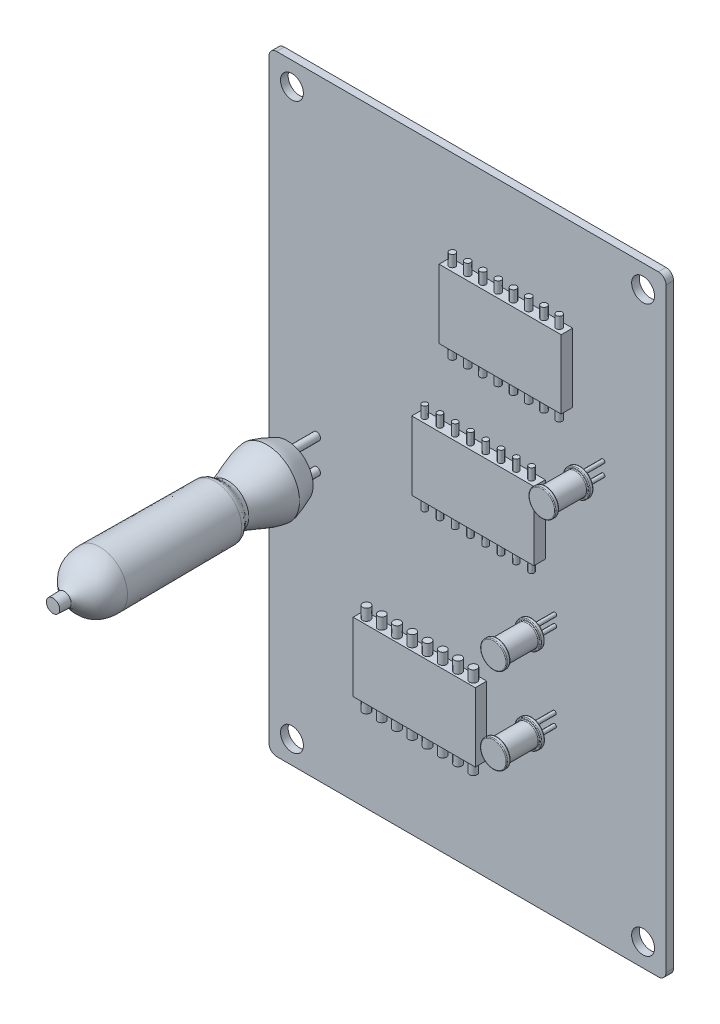
SolidWorks part; units mm, degrees
ref_plane "Plan de face" through (0, 0, 0) normal (0, 0, 1) x (1, 0, 0)
ref_plane "Plan de dessus" through (0, 0, 0) normal (0, 1, 0) x (1, 0, 0)
ref_plane "Plan de droite" through (0, 0, 0) normal (1, 0, 0) x (0, 0, -1)
sketch "Esquisse1" plane through (0, 0, 0) normal (0, 0, 1) x (1, 0, 0)
  line L0 (0, 49.3082) -> (0, -52.8302) construction
  line L1 (50.7838, 0) -> (-60.1596, 0) construction
  line L2 (-25, 40) -> (25, 40)
  line L3 (26, 39) -> (26, -39)
  line L4 (-26, 39) -> (-26, -39)
  line L5 (-25, -40) -> (25, -40)
  circle A0 centre (-23, 37) radius 1.5
  circle A1 centre (23, 37) radius 1.5
  circle A2 centre (23, -37) radius 1.5
  circle A3 centre (-23, -37) radius 1.5
  arc A4 (-25, -40) -> (-26, -39) centre (-25, -39) cw
  arc A5 (25, -40) -> (26, -39) centre (25, -39) ccw
  arc A6 (25, 40) -> (26, 39) centre (25, 39) cw
  arc A7 (-26, 39) -> (-25, 40) centre (-25, 39) cw
  point P8 (0, -40)
  point P10 (0, 40)
  point P11 (-26, 0)
  point P12 (26, 0)
  point P23 (-26, -40)
  point P26 (26, -40)
  point P29 (26, 40)
  point P32 (-26, 40)
  dimension "D2" = 3
  dimension "D1" = 1
extrude "Boss.-Extru.1" add sketch "Esquisse1" along normal blind 1
sketch3d "Esquisse3D1"
  line L0 (-19.7618, -3.0052, 3.4506) -> (-19.7618, -3.0052, 38.1154) construction
ref_plane "Plan1" through (-19.7618, 0, 0) normal (-1, 0, 0) x (0, 0, 1)
sketch "Esquisse2" plane through (-19.7618, 0, 0) normal (-1, 0, 0) x (0, 0, 1)
  line L0 (38.1154, -3.0052) -> (3.4506, -3.0052) construction
  line L1 (4.8485, -6.3885) -> (4.8485, -3.0052)
  line L2 (35.5477, -3.0052) -> (4.8485, -3.0052)
  spline S0 degree 1 poles (35.5477, -3.0052) (35.531, -3.8812) knots 0 0 1 1
  spline S1 degree 2 poles (35.531, -3.8812) (34.9031, -3.9149) (34.078, -3.932) knots 0 0 0 1 1 1
  spline S2 degree 3 poles (34.078, -3.932) (32.9893, -4.1971) (32.7481, -6.6831) (29.4085, -6.6295) knots 0 0 0 0 1 1 1 1
  spline S3 degree 1 poles (29.4085, -6.6295) (14.3307, -6.5217) knots 0 0 1 1
  spline S4 degree 3 poles (14.3307, -6.5217) (13.438, -6.5319) (13.6441, -5.8174) (12.6297, -5.7462) knots 0 0 0 0 1 1 1 1
  spline S5 degree 3 poles (12.6297, -5.7462) (11.6687, -5.8352) (9.4972, -7.0557) (7.5104, -7.2675) knots 0 0 0 0 1 1 1 1
  spline S6 degree 3 poles (7.5104, -7.2675) (6.8891, -7.2309) (5.3946, -6.5858) (4.8485, -6.3885) knots 0 0 0 0 1 1 1 1
revolve "Révolution1" add sketch "Esquisse2" angle 360 about L2
sketch "Esquisse3" plane through (0, 0, 4.8485) normal (0, 0, -1) x (-1, 0, 0)
  line L0 (19.7618, -6.3885) -> (19.7618, 0.5651) construction
  line L1 (23.0053, -3.0052) -> (16.3785, -3.0052) construction
  circle A0 centre (19.7618, -3.0052) radius 3.3833 construction
  circle A1 centre (19.7618, -1.023) radius 0.5
  circle A2 centre (19.7618, -4.9874) radius 0.5
  dimension "D1" = 1
extrude "Boss.-Extru.2" add sketch "Esquisse3" along normal blind 5
sketch "Esquisse4" plane through (0, 0, 1) normal (0, 0, 1) x (1, 0, 0)
  line L1 (13.7698, 27.9997) -> (-2.2302, 27.9997)
  line L2 (13.7698, 27.9997) -> (13.7698, 18.9997)
  line L3 (13.7698, 18.9997) -> (-2.2302, 18.9997)
  line L4 (-2.2302, 27.9997) -> (-2.2302, 18.9997)
  line L5 (10.1949, 9) -> (-5.8051, 9)
  line L6 (10.1949, 9) -> (10.1949, 0)
  line L7 (10.1949, 0) -> (-5.8051, 0)
  line L8 (-5.8051, 9) -> (-5.8051, 0)
  line L9 (2.5156, -17.6757) -> (-13.4844, -17.6757)
  line L10 (2.5156, -17.6757) -> (2.5156, -26.679)
  line L11 (2.5156, -26.679) -> (-13.4844, -26.679)
  line L12 (-13.4844, -17.6757) -> (-13.4844, -26.679)
  dimension "D1" = 9.0033
  dimension "D2" = 9
  dimension "D3" = 9
  dimension "D4" = 16
  dimension "D5" = 16
  dimension "D6" = 16
extrude "Boss.-Extru.3" add sketch "Esquisse4" along normal blind 1.5
sketch "Esquisse5" plane through (0, -26.679, 0) normal (0, -1, 0) x (1, 0, 0)
  line L1 (2.5156, 1.75) -> (-5.4844, 1.75) construction
  line L2 (2.5156, 2.5) -> (2.5156, 1) construction
  circle A0 centre (-4.4844, 1.75) radius 0.5
  circle A1 centre (-2.4844, 1.75) radius 0.5
  circle A2 centre (-0.4844, 1.75) radius 0.5
  circle A3 centre (1.5156, 1.75) radius 0.5
  circle A4 centre (-12.4844, 1.75) radius 0.5
  circle A5 centre (-10.4844, 1.75) radius 0.5
  circle A6 centre (-8.4844, 1.75) radius 0.5
  circle A7 centre (-6.4844, 1.75) radius 0.5
  dimension "D3" = 4
extrude "Boss.-Extru.4" add sketch "Esquisse5" along normal blind 1.5 and the other way blind 10.5
sketch "Esquisse6" plane through (0, 0, 0) normal (0, -1, 0) x (1, 0, 0)
  line L0 (2.1949, 5.3342) -> (2.1949, -1.5605) construction
  line L1 (10.9215, 1.8041) -> (1.2414, 1.8041) construction
  circle A0 centre (3.1949, 1.8041) radius 0.3538
  circle A1 centre (5.1949, 1.8041) radius 0.3538
  circle A2 centre (7.1949, 1.8041) radius 0.3538
  circle A3 centre (9.1949, 1.8041) radius 0.3538
  circle A4 centre (-4.8051, 1.8041) radius 0.3538
  circle A5 centre (-2.8051, 1.8041) radius 0.3538
  circle A6 centre (-0.8051, 1.8041) radius 0.3538
  circle A7 centre (1.1949, 1.8041) radius 0.3538
  dimension "D1" = 1
  dimension "D2" = 4
extrude "Boss.-Extru.5" add sketch "Esquisse6" along normal blind 1.5 and the other way blind 10.5
sketch "Esquisse7" plane through (0, 18.9997, 0) normal (0, -1, 0) x (1, 0, 0)
  line L0 (5.7698, 4.6078) -> (5.7698, -2.5835) construction
  line L1 (15.0689, 1.75) -> (4.3918, 1.75) construction
  circle A0 centre (6.7698, 1.75) radius 0.4
  circle A1 centre (8.7698, 1.75) radius 0.4
  circle A2 centre (10.7698, 1.75) radius 0.4
  circle A3 centre (12.7698, 1.75) radius 0.4
  circle A4 centre (-1.2302, 1.75) radius 0.4
  circle A5 centre (0.7698, 1.75) radius 0.4
  circle A6 centre (2.7698, 1.75) radius 0.4
  circle A7 centre (4.7698, 1.75) radius 0.4
  dimension "D1" = 0.8
  dimension "D2" = 1
  dimension "D3" = 4
extrude "Boss.-Extru.6" add sketch "Esquisse7" along normal blind 1.5 and the other way blind 10.5
sketch "Esquisse8" plane through (0, 0, 1) normal (0, 0, 1) x (1, 0, 0)
  circle A0 centre (11.3866, -17.5433) radius 1.75
  circle A1 centre (11.3866, -6.2891) radius 1.725
  circle A2 centre (17.7419, 14.1008) radius 1.75
  dimension "D1" = 3.5
  dimension "D2" = 3.45
  dimension "D3" = 3.5
extrude "Boss.-Extru.7" add sketch "Esquisse8" along normal blind 0.5 from offset 3 separate body
sketch "Esquisse9" plane through (0, 0, 4.5) normal (0, 0, 1) x (1, 0, 0)
  circle A9 centre (17.7419, 14.1008) radius 1.45
  circle A10 centre (11.3866, -6.2891) radius 1.425
  circle A11 centre (11.3866, -17.5433) radius 1.45
extrude "Boss.-Extru.8" add sketch "Esquisse9" along normal blind 4
sketch "Esquisse10" plane through (0, 0, 8.5) normal (0, 0, 1) x (1, 0, 0)
  circle A6 centre (11.3866, -6.2891) radius 1.725
  circle A7 centre (11.3866, -17.5433) radius 1.75
  circle A8 centre (17.7419, 14.1008) radius 1.75
extrude "Boss.-Extru.9" add sketch "Esquisse10" along normal blind 0.5
fillet "Congé1" radius 0.1 4 edges at (19.4919, 14.1008, 8.5) (19.4919, 14.1008, 9) (19.4919, 14.1008, 4) (19.4919, 14.1008, 4.5)
fillet "Congé2" radius 0.1 4 edges at (13.1116, -6.2891, 8.5) (13.1116, -6.2891, 9) (13.1116, -6.2891, 4) (13.1116, -6.2891, 4.5)
fillet "Congé3" radius 0.1 4 edges at (13.1366, -17.5433, 4) (13.1366, -17.5433, 4.5) (13.1366, -17.5433, 8.5) (13.1366, -17.5433, 9)
sketch "Esquisse11" plane through (0, 0, 4) normal (0, 0, -1) x (-1, 0, 0)
  line L0 (-17.7419, 15.7508) -> (-17.7419, 12.4508) construction
  line L1 (-19.3919, 14.1008) -> (-16.0919, 14.1008) construction
  circle A0 centre (-17.7419, 14.1008) radius 1.65 construction
  circle A1 centre (-17.7419, 13.3045) radius 0.25
  circle A2 centre (-17.7419, 14.8971) radius 0.25
  dimension "D1" = 0.5
extrude "Boss.-Extru.10" add sketch "Esquisse11" along normal up to next (3 mm away)
fillet "Congé4" radius 0.1 2 edges at (19.1919, 14.1008, 4.5) (19.1919, 14.1008, 8.5)
fillet "Congé5" radius 0.1 2 edges at (12.8116, -6.2891, 4.5) (12.8116, -6.2891, 8.5)
fillet "Congé6" radius 0.1 2 edges at (12.8366, -17.5433, 4.5) (12.8366, -17.5433, 8.5)
sketch "Esquisse12" plane through (0, 0, 4) normal (0, 0, -1) x (-1, 0, 0)
  line L0 (-11.3244, -4.6653) -> (-11.4801, -7.9114) construction
  line L1 (-13.0116, -6.2891) -> (-9.844, -6.2891) construction
  circle A0 centre (-11.3866, -6.2891) radius 1.625 construction
  circle A1 centre (-11.4335, -6.9392) radius 0.25
  circle A2 centre (-11.4335, -5.639) radius 0.25
  dimension "D1" = 0.5
extrude "Boss.-Extru.11" add sketch "Esquisse12" along normal up to next
sketch "Esquisse14" plane through (0, 0, 4) normal (0, 0, -1) x (-1, 0, 0)
  line L0 (-13.0366, -17.5433) -> (-9.6844, -17.5751) construction
  line L1 (-11.3866, -15.8933) -> (-11.3866, -19.1933) construction
  circle A0 centre (-11.3866, -17.5433) radius 1.65 construction
  circle A1 centre (-11.3866, -18.3044) radius 0.25
  circle A2 centre (-11.3724, -16.8136) radius 0.25
  dimension "D1" = 0.5
extrude "Boss.-Extru.12" add sketch "Esquisse14" along normal up to next
